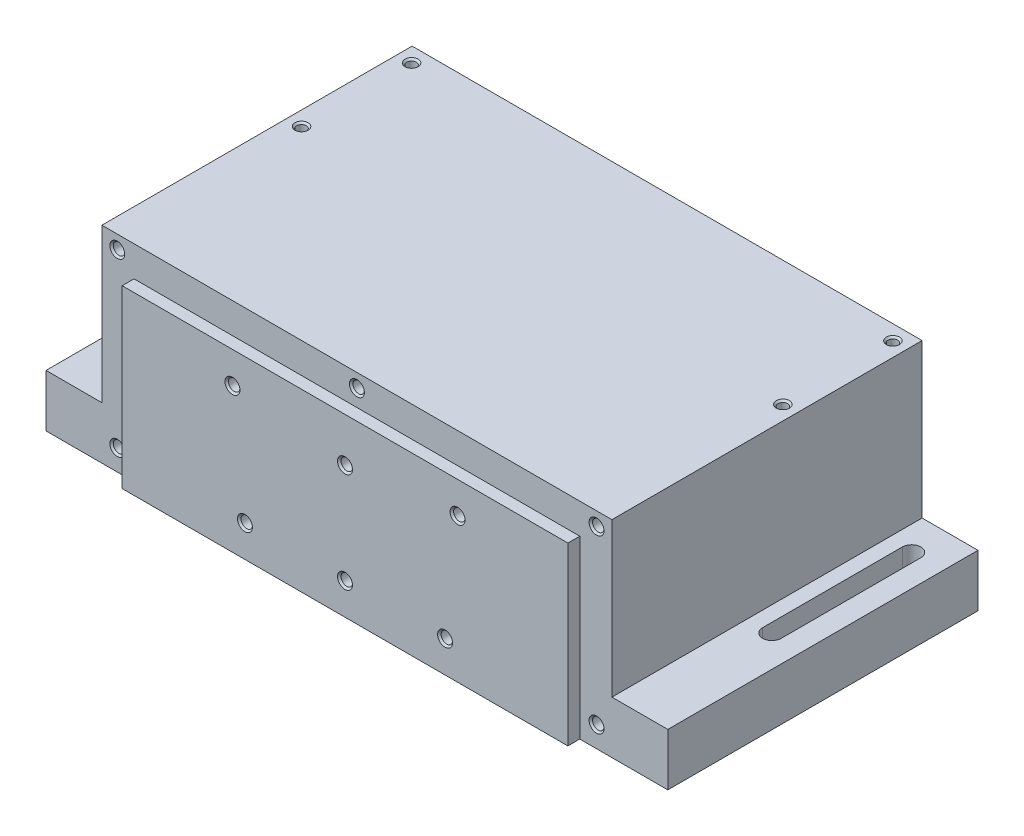
SolidWorks part; units mm, degrees
material "6061-T6 Al"
ref_plane "Front" through (0, 0, 0) normal (0, 0, 1) x (1, 0, 0)
ref_plane "Top" through (0, 0, 0) normal (0, 1, 0) x (1, 0, 0)
ref_plane "Right" through (0, 0, 0) normal (1, 0, 0) x (0, 0, -1)
sketch "Sketch1" plane through (0, 0, 0) normal (0, 0, 1) x (1, 0, 0)
  line L0 (-92.71, 2.54) -> (92.71, 2.54)
  line L1 (92.71, 2.54) -> (92.71, 0)
  line L2 (92.71, 0) -> (113.03, 0)
  line L3 (113.03, 0) -> (113.03, 19.05)
  line L4 (113.03, 19.05) -> (92.71, 19.05)
  line L5 (92.71, 19.05) -> (92.71, 74.93)
  line L6 (92.71, 74.93) -> (-92.71, 74.93)
  line L7 (0, 74.93) -> (0, 2.54) construction
  line L8 (-92.71, 19.05) -> (-92.71, 74.93)
  line L9 (-113.03, 19.05) -> (-92.71, 19.05)
  line L10 (-113.03, 0) -> (-113.03, 19.05)
  line L11 (-92.71, 0) -> (-113.03, 0)
  line L12 (-92.71, 2.54) -> (-92.71, 0)
  dimension "D1" = 226.06
  dimension "D3" = 2.54
  dimension "D4" = 185.42
  dimension "D5" = 19.05
  dimension "D6" = 74.93
extrude "Boss-Extrude1" add sketch "Sketch1" against normal blind 50.8
hole_wizard "#6-32 Tapped Hole1" positions "Sketch4" profile "Sketch3" tap size "#6-32" standard "ANSI Inch"
sketch "Sketch4" plane through (0, 74.93, 0) normal (0, 1, 0) x (1, 0, 0)
  line L0 (87.503, 45.4025) -> (0, 25.4) construction
  line L3 (0, 25.4) -> (-87.503, 5.3975) construction
  line L4 (0, 25.4) -> (92.71, 25.4) construction
  line L6 (92.71, 50.8) -> (92.71, 0) construction
  point P0 (-87.503, 45.4025)
  point P2 (-87.503, 5.3975)
  point P4 (87.503, 5.3975)
  point P6 (87.503, 45.4025)
  dimension "D1" = 175.006
  dimension "D2" = 40.005
sketch "Sketch3" plane through (-87.503, 74.93, -45.4025) normal (1, 0, 0) x (0, 0, 1)
  line L0 (0, 0) -> (0, 14.4271)
  line L1 (0, 14.4271) -> (1.3525, 13.6144)
  line L2 (1.3525, 13.6144) -> (1.3525, 9.652)
  line L3 (1.3525, 9.652) -> (1.7526, 9.652)
  line L5 (1.7526, 9.652) -> (1.7526, 0.635)
  line L6 (1.7526, 0.635) -> (2.3876, 0)
  line L7 (2.3876, 0) -> (0, 0)
  line L8 (-1.7526, 0.635) -> (-2.3876, 0) construction
  line L10 (0, 14.4271) -> (-1.3526, 13.6144) construction
  line L11 (0, -6.35) -> (0, 107.95) construction
  dimension "Tap Drill Dia." = 2.7051
  dimension "Tap Drill Depth" = 13.6144
  dimension "Thread Major Dia." = 3.5052
  dimension "Thread Depth" = 9.652
  dimension "Near C'Sink Dia." = 4.7752
  dimension "Near C'Sink Angle" = 90
  dimension "Drill Angle" = 118
sketch "Sketch5" plane through (0, 0, 0) normal (0, 0, 1) x (1, 0, 0)
  line L0 (0, 74.93) -> (0, 2.54) construction
  line L1 (0, 74.93) -> (0, 2.54) construction
  line L2 (92.71, 74.93) -> (-92.71, 74.93) construction
  line L3 (92.71, 74.93) -> (-92.71, 74.93)
  line L4 (92.71, 74.93) -> (92.71, 19.05)
  line L5 (113.03, 19.05) -> (113.03, 0)
  line L6 (-92.71, 19.05) -> (-92.71, 74.93)
  line L8 (-92.71, 74.93) -> (-92.71, 19.05) construction
  line L9 (-92.71, 19.05) -> (-113.03, 19.05) construction
  line L10 (-113.03, 19.05) -> (-113.03, 0) construction
  line L11 (-113.03, 0) -> (-92.71, 0) construction
  line L12 (-92.71, 19.05) -> (-113.03, 19.05)
  line L13 (-113.03, 19.05) -> (-113.03, 0)
  line L14 (-113.03, 0) -> (113.03, 0)
  line L15 (92.71, 19.05) -> (113.03, 19.05)
extrude "Boss-Extrude2" add sketch "Sketch5" along normal blind 61.976
sketch "Sketch16" plane through (0, 19.05, 0) normal (0, 1, 0) x (1, 0, 0)
  line L0 (0, 25.4) -> (0, 50.8) construction
  line L2 (-104.9782, 38.1) -> (-104.9782, -12.7)
  line L3 (-98.2218, 38.1) -> (-98.2218, -12.7)
  line L6 (-101.6, 38.1) -> (-101.6, 12.7) construction
  line L8 (-101.6, 12.7) -> (-101.6, -12.7) construction
  line L12 (104.9782, 38.1) -> (104.9782, -12.7)
  line L13 (98.2218, 38.1) -> (98.2218, -12.7)
  line L16 (92.71, 50.8) -> (-92.71, 50.8) construction
  line L17 (0, 25.4) -> (92.71, 25.4) construction
  arc A0 (-104.9782, 38.1) -> (-98.2218, 38.1) centre (-101.6, 38.1) cw
  arc A1 (-98.2218, -12.7) -> (-104.9782, -12.7) centre (-101.6, -12.7) cw
  arc A6 (98.2218, -12.7) -> (104.9782, -12.7) centre (101.6, -12.7) ccw
  arc A7 (104.9782, 38.1) -> (98.2218, 38.1) centre (101.6, 38.1) ccw
  dimension "D5" = 203.2
  dimension "D1" = 12.7
  dimension "D2" = 6.7564
  dimension "D4" = 50.8
extrude "Cut-Extrude2" cut sketch "Sketch16" against normal through all
hole_wizard "#8-32 Tapped Hole1" positions "Sketch12" profile "Sketch11" tap size "#8-32" standard "ANSI Inch"
sketch "Sketch12" plane through (0, 0, 61.976) normal (0, 0, 1) x (1, 0, 0)
  line L0 (0, 74.93) -> (0, 2.54) construction
  line L1 (0, 74.93) -> (0, 2.54) construction
  line L2 (0, 38.735) -> (-87.122, 38.735) construction
  line L3 (92.71, 74.93) -> (-92.71, 74.93) construction
  line L4 (-92.71, 74.93) -> (-92.71, 19.05) construction
  line L5 (-113.03, 0) -> (113.03, 0) construction
  line L6 (92.71, 74.93) -> (-92.71, 74.93) construction
  line L7 (-92.71, 2.54) -> (92.71, 2.54) construction
  point P0 (-87.122, 69.977)
  point P2 (-87.122, 7.62)
  point P11 (87.122, 7.62)
  point P12 (87.122, 69.977)
  point P19 (0, 69.977)
  dimension "D1" = 4.953
  dimension "D2" = 5.588
  dimension "D3" = 62.357
  dimension "D4" = 174.244
  dimension "D5" = 7.62
sketch "Sketch11" plane through (-87.122, 69.977, 61.976) normal (1, 0, 0) x (0, -1, 0)
  line L0 (0, 0) -> (0, 17.7002)
  line L1 (0, 17.7002) -> (1.7272, 16.6624)
  line L2 (1.7272, 16.6624) -> (1.7272, 12.7)
  line L3 (1.7272, 12.7) -> (2.0828, 12.7)
  line L5 (2.0828, 12.7) -> (2.0828, 0.635)
  line L6 (2.0828, 0.635) -> (2.7178, 0)
  line L7 (2.7178, 0) -> (0, 0)
  line L8 (-2.0828, 0.635) -> (-2.7178, 0) construction
  line L10 (0, 17.7002) -> (-1.7272, 16.6624) construction
  line L11 (0, -6.35) -> (0, 107.95) construction
  dimension "Tap Drill Dia." = 3.4544
  dimension "Tap Drill Depth" = 16.6624
  dimension "Thread Major Dia." = 4.1656
  dimension "Thread Depth" = 12.7
  dimension "Near C'Sink Dia." = 5.4356
  dimension "Near C'Sink Angle" = 90
  dimension "Drill Angle" = 118
sketch "Sketch13" plane through (0, 0, 61.976) normal (0, 0, 1) x (1, 0, 0)
  line L0 (-81.026, 0) -> (-81.026, 63.881)
  line L2 (-81.026, 63.881) -> (81.026, 63.881)
  line L3 (81.026, 63.881) -> (81.026, 0)
  line L4 (81.026, 0) -> (-81.026, 0)
  line L5 (0, 63.881) -> (0, 0) construction
  line L6 (-113.03, 0) -> (113.03, 0) construction
  dimension "D1" = 6.096
  dimension "D2" = 6.096
extrude "Boss-Extrude4" add sketch "Sketch13" along normal blind 4.318
hole_wizard "#8-32 Tapped Hole2" positions "Sketch8" profile "Sketch7" tap size "#8-32" standard "ANSI Inch"
sketch "Sketch8" plane through (-53.4499, 7.476, 66.294) normal (0, 0, 1) x (1, 0, 0)
  line L0 (53.4499, 67.454) -> (53.4499, -4.936) construction
  line L1 (53.4499, 56.405) -> (53.4499, 44.9242) construction
  line L8 (134.4759, 56.405) -> (-27.5761, 56.405) construction
  line L13 (53.4499, 4.0048) -> (53.4499, -7.476) construction
  line L14 (134.4759, -7.476) -> (134.4759, 56.405) construction
  point P0 (12.5305, 44.9242)
  point P2 (17.0771, 4.0048)
  point P8 (89.8227, 4.0048)
  point P9 (94.3693, 44.9242)
  point P56 (53.4499, 4.0048)
  point P69 (53.4499, 40.3776)
  dimension "D1" = 40.9194
  dimension "D2" = 81.8388
  dimension "D3" = 4.5466
  dimension "D4" = 11.4808
  dimension "D5" = 36.3728
  dimension "D6" = 77.2922
  dimension "D7" = 40.9194
  dimension "D8" = 40.1066
sketch "Sketch7" plane through (-40.9194, 52.4002, 66.294) normal (1, 0, 0) x (0, -1, 0)
  line L0 (0, 0) -> (0, 17.7002)
  line L1 (0, 17.7002) -> (1.7272, 16.6624)
  line L2 (1.7272, 16.6624) -> (1.7272, 12.7)
  line L3 (1.7272, 12.7) -> (2.0828, 12.7)
  line L5 (2.0828, 12.7) -> (2.0828, 0.635)
  line L6 (2.0828, 0.635) -> (2.7178, 0)
  line L7 (2.7178, 0) -> (0, 0)
  line L8 (-2.0828, 0.635) -> (-2.7178, 0) construction
  line L10 (0, 17.7002) -> (-1.7272, 16.6624) construction
  line L11 (0, -6.35) -> (0, 107.95) construction
  dimension "Tap Drill Dia." = 3.4544
  dimension "Tap Drill Depth" = 16.6624
  dimension "Thread Major Dia." = 4.1656
  dimension "Thread Depth" = 12.7
  dimension "Near C'Sink Dia." = 5.4356
  dimension "Near C'Sink Angle" = 90
  dimension "Drill Angle" = 118
sketch "Sketch17" plane through (0, 2.54, 0) normal (0, -1, 0) x (1, 0, 0)
  line L0 (-92.71, 0) -> (92.71, 0) construction
  line L1 (-92.71, 0) -> (92.71, 0)
  line L2 (-92.71, 0) -> (-92.71, 49.403)
  line L3 (-83.185, 58.928) -> (83.185, 58.928)
  line L4 (92.71, 49.403) -> (92.71, 0)
  line L5 (-113.03, 61.976) -> (-81.026, 61.976) construction
  arc A0 (83.185, 58.928) -> (92.71, 49.403) centre (83.185, 49.403) cw
  arc A1 (-92.71, 49.403) -> (-83.185, 58.928) centre (-83.185, 49.403) cw
  dimension "D2" = 9.525
  dimension "D1" = 3.048
extrude "Cut-Extrude3" cut sketch "Sketch17" along normal through all
hole_wizard "1/4-20 Tapped Hole1" positions "Sketch19" profile "Sketch18" tap size "1/4-20" standard "ANSI Inch"
sketch "Sketch19" plane through (0, 0, -50.8) normal (0, 0, -1) x (-1, 0, 0)
  line L0 (-25.4, 38.1) -> (0, 38.1) construction
  line L1 (0, 38.1) -> (25.4, 38.1) construction
  line L2 (0, 38.1) -> (0, 2.54) construction
  line L3 (92.71, 2.54) -> (-92.71, 2.54) construction
  line L4 (-92.71, 0) -> (-113.03, 0) construction
  point P0 (-25.4, 38.1)
  point P2 (25.4, 38.1)
  dimension "D1" = 38.1
  dimension "D2" = 50.8
sketch "Sketch18" plane through (25.4, 38.1, -50.8) normal (1, 0, 0) x (0, 1, 0)
  line L0 (0, 0) -> (0, 20.5838)
  line L1 (0, 20.5838) -> (2.5527, 19.05)
  line L2 (2.5527, 19.05) -> (2.5527, 12.7)
  line L3 (2.5527, 12.7) -> (3.175, 12.7)
  line L5 (3.175, 12.7) -> (3.175, 0.762)
  line L6 (3.175, 0.762) -> (3.937, 0)
  line L7 (3.937, 0) -> (0, 0)
  line L8 (-3.175, 0.762) -> (-3.937, 0) construction
  line L10 (0, 20.5838) -> (-2.5527, 19.05) construction
  line L11 (0, -6.35) -> (0, 107.95) construction
  dimension "Tap Drill Dia." = 5.1054
  dimension "Tap Drill Depth" = 19.05
  dimension "Thread Major Dia." = 6.35
  dimension "Thread Depth" = 12.7
  dimension "Near C'Sink Dia." = 7.874
  dimension "Near C'Sink Angle" = 90
  dimension "Drill Angle" = 118
